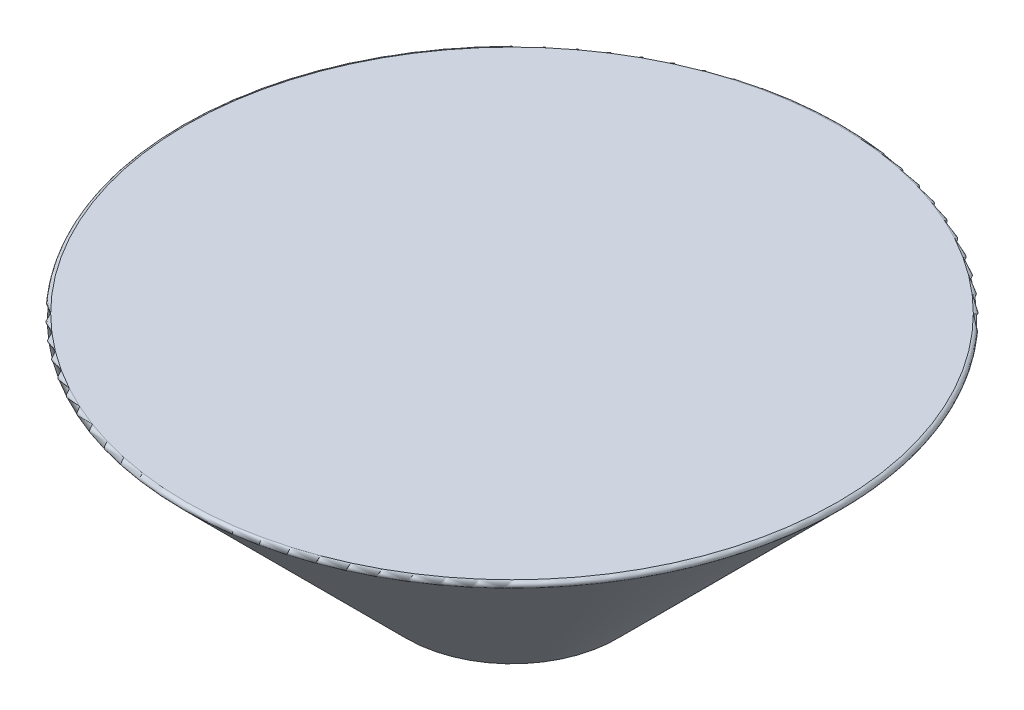
SolidWorks part; units mm, degrees
ref_plane "Front Plane" through (0, 0, 0) normal (0, 0, 1) x (1, 0, 0)
ref_plane "Top Plane" through (0, 0, 0) normal (0, 1, 0) x (1, 0, 0)
ref_plane "Right Plane" through (0, 0, 0) normal (1, 0, 0) x (0, 0, -1)
sketch "Sketch1" plane through (0, 0, 0) normal (0, 0, 1) x (1, 0, 0)
  line L0 (0, 0) -> (0, -39.64)
  line L1 (0, -44.7868) -> (0, 44.7868) construction
  line L2 (0, 0) -> (50, 0)
  line L3 (55, 0) -> (-55, 0) construction
  line L4 (4.3829, 0) -> (4.3829, -14.6) construction
  line L5 (0, -14.8395) -> (15.727, -34.273) construction
  line L6 (50, 0) -> (15.727, -34.273)
  arc A0 (0, -39.64) -> (15.727, -34.273) centre (0, -13.914) ccw
  dimension "D1" = 39.64
  dimension "D2" = 50
  dimension "D3" = 14.6
  dimension "D4" = 25
revolve "Revolve1" add sketch "Sketch1" angle 360 about L0
fillet "Fillet3" radius 0.5 1 edges at (0, 0, 50)
